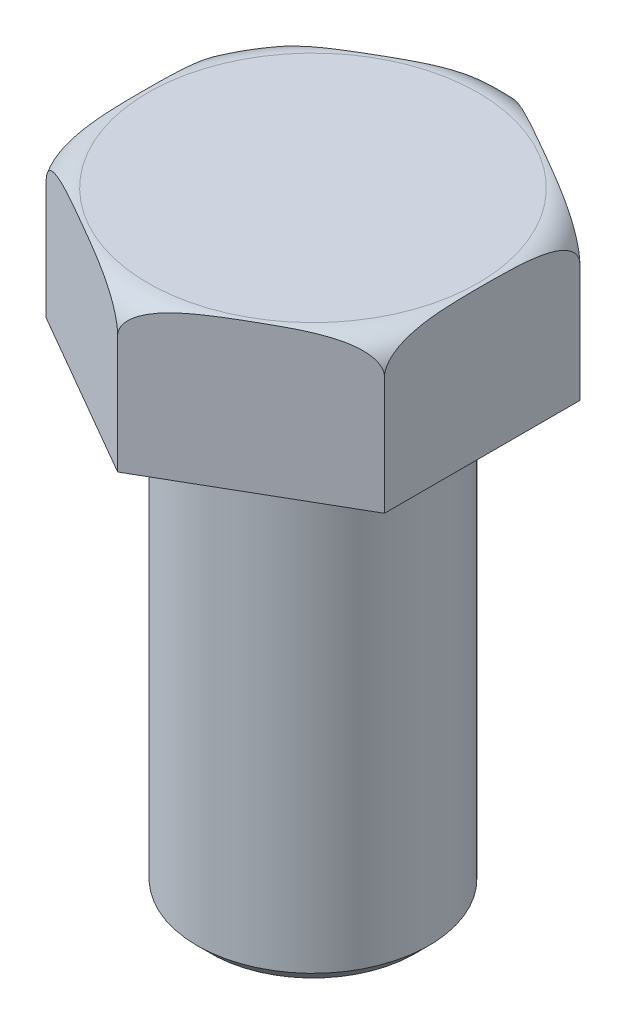
SolidWorks part; units mm, degrees
material "AISI 1020"
ref_plane "Front" through (0, 0, 0) normal (0, 0, 1) x (1, 0, 0)
ref_plane "Top" through (0, 0, 0) normal (0, 1, 0) x (1, 0, 0)
ref_plane "Right" through (0, 0, 0) normal (1, 0, 0) x (0, 0, -1)
sketch "Sketch1" plane through (0, 0, 0) normal (0, 1, 0) x (1, 0, 0)
  line L1 (0, 10.6975) -> (-9.2643, 5.3487)
  line L2 (-9.2643, 5.3487) -> (-9.2643, -5.3487)
  line L3 (-9.2643, -5.3487) -> (0, -10.6975)
  line L4 (0, -10.6975) -> (9.2643, -5.3487)
  line L5 (9.2643, -5.3487) -> (9.2643, 5.3487)
  line L6 (9.2643, 5.3487) -> (0, 10.6975)
  circle A0 centre (0, 0) radius 10.6975 construction
extrude "Extrude1" add sketch "Sketch1" along normal blind 8.128
sketch "Sketch3" plane through (0, 0, 0) normal (0, -1, 0) x (1, 0, 0)
  circle A0 centre (0, 0) radius 6.35
  dimension "D1" = 12.7
extrude "Extrude2" add sketch "Sketch3" along normal blind 25.4
cosmetic thread "Cosmetic Thread1" parameters "D2"=11.1125
sketch "Sketch2" plane through (0, 0, 0) normal (1, 0, 0) x (0, 0, -1)
  line L0 (9.038, 8.128) -> (10.6975, 8.128)
  line L1 (5.3487, 8.128) -> (10.6975, 8.128) construction
  line L2 (10.6975, 6.4685) -> (10.6975, 8.128)
  line L3 (10.6975, 8.128) -> (10.6975, 0) construction
  arc A0 (9.038, 8.128) -> (10.6975, 6.4685) centre (9.038, 6.4685) cw
  dimension "D1" = 1.6595
revolve "Cut-Revolve1" cut sketch "Sketch2" angle 360 about axis through (0, -25.4, 0) along (0, 1, 0)
chamfer "Chamfer1" distance 0.762 angle 45 1 edges at (0, -25.4, -6.35)
